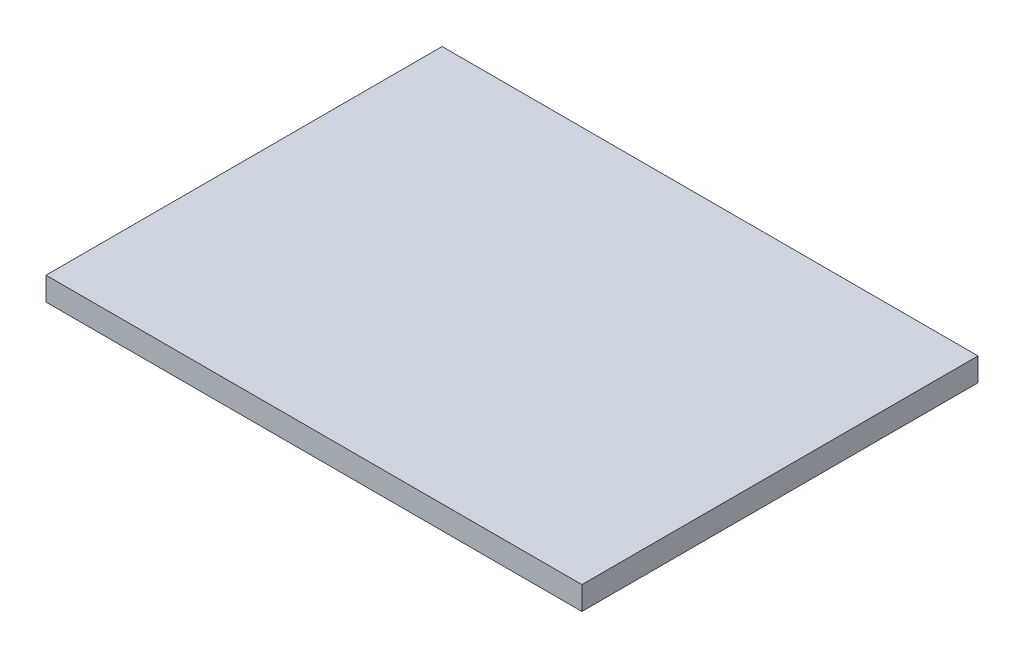
SolidWorks part; units mm, degrees
ref_plane "Plan de face" through (0, 0, 0) normal (0, 0, 1) x (1, 0, 0)
ref_plane "Plan de dessus" through (0, 0, 0) normal (0, 1, 0) x (1, 0, 0)
ref_plane "Plan de droite" through (0, 0, 0) normal (1, 0, 0) x (0, 0, -1)
sketch "Esquisse1" plane through (0, 0, 0) normal (0, 1, 0) x (1, 0, 0)
  line L1 (0, 0) -> (46, 0)
  line L2 (0, 0) -> (0, 34)
  line L3 (0, 34) -> (46, 34)
  line L4 (46, 0) -> (46, 34)
  dimension "D1" = 46
  dimension "D2" = 34
extrude "Boss.-Extru.1" add sketch "Esquisse1" along normal blind 2
